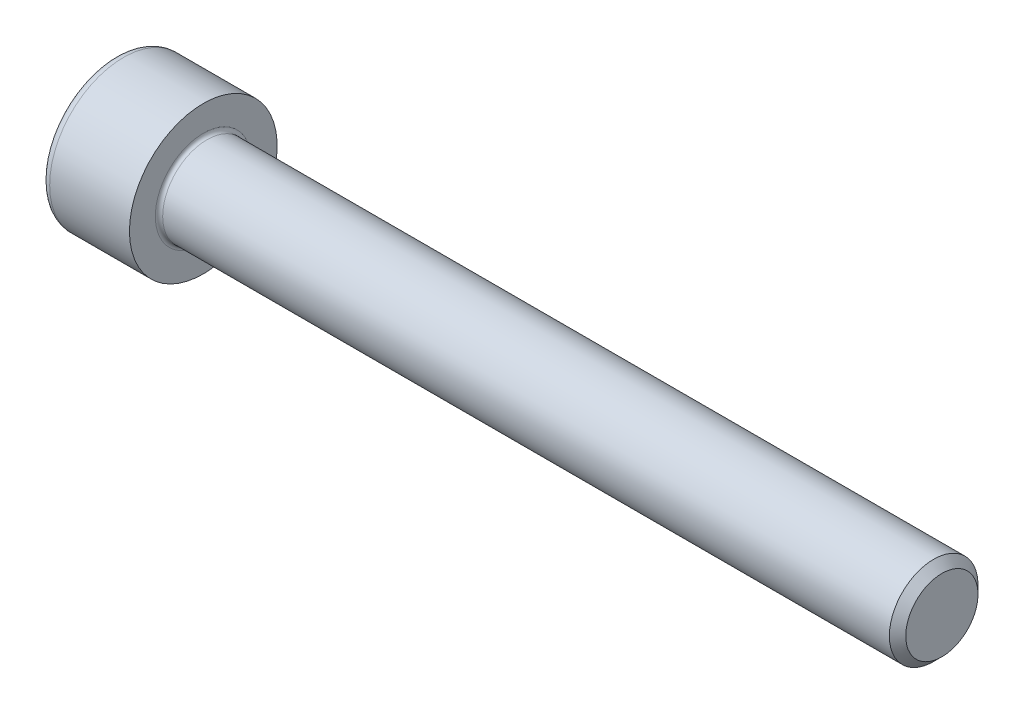
SolidWorks part; units mm, degrees
revolve "Base-Revolve" add sketch "BodySke"
sketch "BodySke" plane through (0, 0, 0) normal (0, 0, 1) x (1, 0, 0)
  line L0 (0, 0) -> (0, 5)
  line L1 (0, 5) -> (6, 5)
  line L2 (6, 5) -> (6, 3)
  line L3 (6, 3) -> (55.4455, 3)
  line L4 (56, 2.4455) -> (56, 0)
  line L5 (56, 0) -> (0, 0)
  line L6 (-31.75, 0) -> (127, 0) construction
  line L8 (56, 2.4455) -> (55.4455, 3)
  line L10 (56, -2.4455) -> (55.4455, -3) construction
  line L11 (7, 9.525) -> (7, 3.175) construction
  line L12 (32, 9.525) -> (32, 3.175) construction
  line L13 (-4, 9.525) -> (-4, 3.175) construction
  dimension "Body_ch_ang" = 45
  dimension "Thread_length" = 60
cosmetic thread "ThreadCosmetic" [suppressed]
fillet "Fillet1" radius 0.25 1 edges at (6, 0, 3)
fillet "Fillet2" radius 0.6 1 edges at (0, 0, 5)
ref_plane "Plane1" through (0, 0, 0) normal (0, 0, 1) x (1, 0, 0)
ref_plane "Plane2" through (0, 0, 0) normal (0, 1, 0) x (1, 0, 0)
ref_plane "Plane3" through (0, 0, 0) normal (1, 0, 0) x (0, 0, -1)
sketch "Sketch2" plane through (0, 0, 0) normal (0, 0, 1) x (1, 0, 0)
  line L0 (0, 2.51) -> (3, 2.51)
  line L1 (3, 2.51) -> (4.4491, 0)
  line L2 (-31.75, 0) -> (127, 0) construction
  line L3 (4.4491, 0) -> (0, 0)
  line L4 (0, 0) -> (0, 2.51)
  line L6 (0, 0) -> (47.625, 0) construction
  dimension "D2" = 60
revolve "Hex-PreBroach" cut sketch "Sketch2" angle 360 about L6
sketch "Sketch3" plane through (0, 0, 0) normal (-1, 0, 0) x (0, 0.5, 0.866)
  line L0 (1.4491, 2.51) -> (-1.4491, 2.51)
  line L1 (-1.4491, 2.51) -> (-2.8983, 0)
  line L2 (1.4491, 2.51) -> (2.8983, 0)
  line L3 (1.4491, -2.51) -> (2.8983, 0)
  line L4 (1.4491, -2.51) -> (-1.4491, -2.51)
  line L5 (-1.4491, -2.51) -> (-2.8983, 0)
extrude "Hex" cut sketch "Sketch3" against normal blind 3
sketch "ThdSchSke" plane through (0, 0, 0) normal (0, 0, 1) x (1, 0, 0)
  line L0 (32, -2.4455) -> (31.6117, -3)
  line L1 (32, -2.4455) -> (32.3883, -3)
  line L2 (32.3883, -3) -> (32.3883, -3.75)
  line L3 (-3.175, 0) -> (5.1513, 0) construction
  line L4 (0, 4.4) -> (0, -4.4) construction
  line L5 (32.3883, -3.75) -> (31.6117, -3.75)
  line L6 (31.6117, -3.75) -> (31.6117, -3)
revolve "ThreadSchematic" [suppressed] cut sketch "ThdSchSke" angle 360 about L3
pattern_linear "ThdSchPat" [suppressed]
equation "\"D2@Sketch3\" = \"Hex_size@Sketch3\" / 2"
equation "\"D1@Sketch3\" = \"Hex_size@Sketch3\" / 2"
equation "\"D1@Sketch2\" = \"Hex_size@Sketch3\" / 2"
equation "\"Thread_minor@ThreadCosmetic\"  =  \"Minor_dia@BodySke\""
equation "\"Depth@Sketch2\" =  \"Key_eng@Hex\""
equation "\"Thread_length@ThreadCosmetic\" = ((sgn( (\"Length@BodySke\" - \"Advance@BodySke\" * 3.0) - \"Thread_nom@BodySke\" )-1)*( (\"Length@BodySke\" - \"Advance@BodySke\" * 3.0) - \"Thread_nom@BodySke\" ))/-2+ \"Thread_nom@BodySke\""
equation "\"Thread_minor@ThdSchSke\" = \"Minor_dia@BodySke\""
equation "\"Diameter@ThdSchSke\" = \"Diameter@BodySke\""
equation "\"Overcut@ThdSchSke\" = \"Diameter@BodySke\" * 1.25"
equation "\"Start@ThdSchSke\" = \"Head_ht@BodySke\" + \"Length@BodySke\" - \"Thread_length@ThreadCosmetic\"  '---Non-countersunk---"
equation "\"Num_threads@ThdSchPat\" = int( \"Thread_length@ThreadCosmetic\" / \"Advance@BodySke\" + 0.999 )  + 1"
equation "\"Advance@ThdSchPat\" = \"Thread_length@ThreadCosmetic\" /  (\"Num_threads@ThdSchPat\" - 1) 'relax it"
equation "\"Num_threads@ThdSchPat\" = \"Num_threads@ThdSchPat\" - sgn( \"Num_threads@ThdSchPat\" - 1) '---chamfered tips only---"
